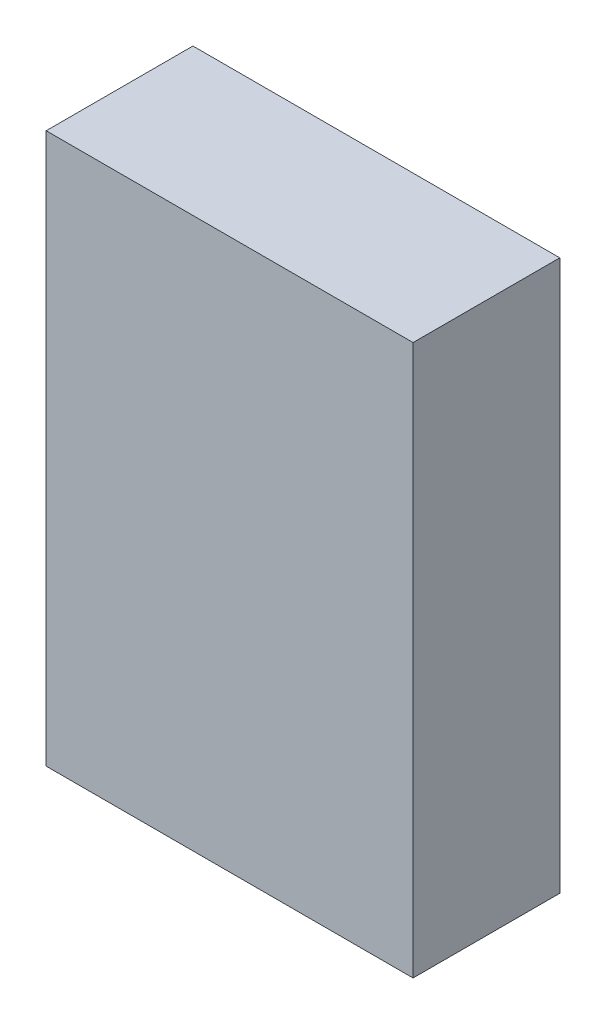
SolidWorks part; units mm, degrees
ref_plane "Front Plane" through (0, 0, 0) normal (0, 0, 1) x (1, 0, 0)
ref_plane "Top Plane" through (0, 0, 0) normal (0, 1, 0) x (1, 0, 0)
ref_plane "Right Plane" through (0, 0, 0) normal (1, 0, 0) x (0, 0, -1)
sketch "Sketch1" plane through (0, 0, 0) normal (0, 0, 1) x (1, 0, 0)
  line L1 (0, 0) -> (50, 0)
  line L2 (0, 0) -> (0, 75)
  line L3 (0, 75) -> (50, 75)
  line L4 (50, 0) -> (50, 75)
  dimension "D1" = 50
  dimension "D2" = 75
extrude "Boss-Extrude1" add sketch "Sketch1" along normal blind 20
